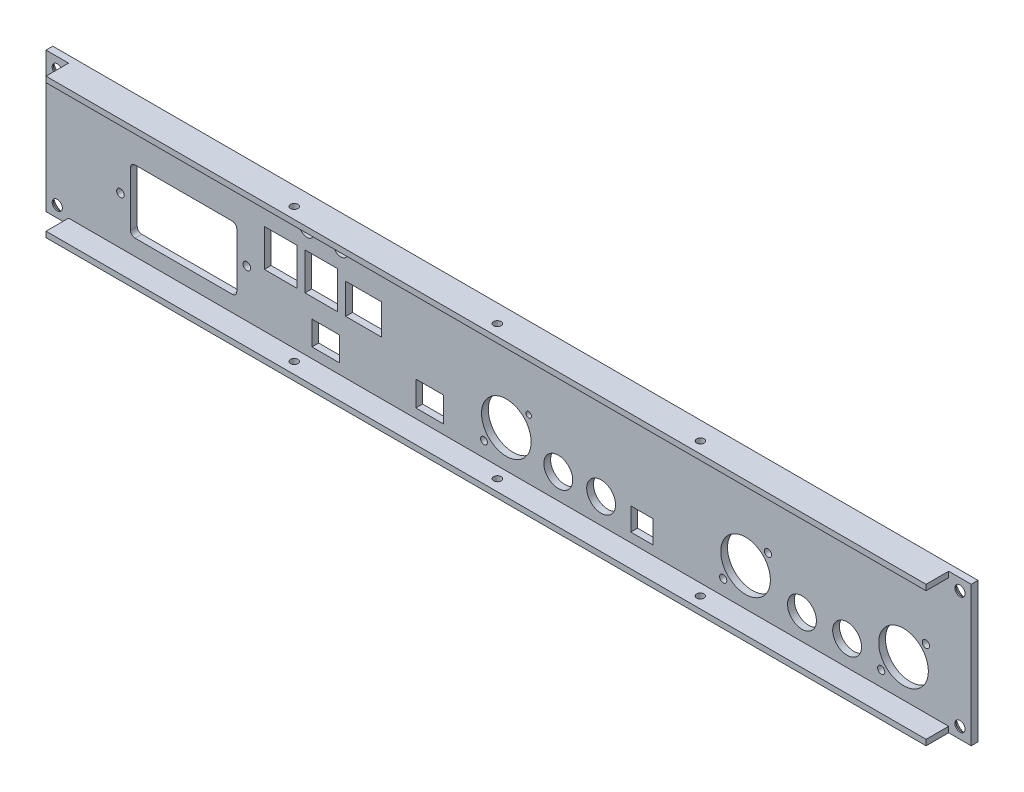
SolidWorks part; units mm, degrees
ref_plane "前基準面" through (0, 0, 0) normal (0, 0, 1) x (1, 0, 0)
ref_plane "上基準面" through (0, 0, 0) normal (0, 1, 0) x (1, 0, 0)
ref_plane "右基準面" through (0, 0, 0) normal (1, 0, 0) x (0, 0, -1)
sketch "草圖1" plane through (0, 0, 0) normal (0, 0, 1) x (1, 0, 0)
  line L1 (-205, -31) -> (205, -31)
  line L2 (-205, -31) -> (-205, 31)
  line L3 (-205, 31) -> (205, 31)
  line L4 (205, -31) -> (205, 31)
  line L5 (-205, -31) -> (205, 31) construction
  line L6 (-205, 31) -> (205, -31) construction
  point P0 (0, 0)
  dimension "D1" = 62
  dimension "D2" = 410
extrude "填料-伸長1" add sketch "草圖1" along normal blind 3
hole_wizard "M4 錐坑平頭螺釘的錐孔1" positions "草圖3" profile "草圖2" countersink size "M4" standard "ISO" end condition through all
sketch "草圖3" plane through (0, 0, 0) normal (0, 0, 1) x (1, 0, 0)
  line L0 (-205, 31) -> (-205, -31) construction
  line L1 (205, -31) -> (205, 31) construction
  line L2 (205, 31) -> (-205, 31) construction
  line L3 (-205, -31) -> (205, -31) construction
  point P0 (-200, 26)
  point P2 (-200, -26)
  point P4 (200, -26)
  point P6 (200, 26)
  dimension "D1" = 5
  dimension "D2" = 5
  dimension "D3" = 5
  dimension "D4" = 5
sketch "草圖2" plane through (-200, 26, 0) normal (1, 0, 0) x (0, 1, 0)
  line L0 (0, 0) -> (0, 3)
  line L1 (0, 3) -> (2.25, 3)
  line L2 (2.25, 3) -> (2.25, 2.45)
  line L3 (2.25, 2.45) -> (4.7, 0)
  line L5 (4.7, 0) -> (0, 0)
  line L6 (-2.25, 2.45) -> (-4.7, 0) construction
  line L11 (0, -6.35) -> (0, 107.95) construction
  dimension "貫穿孔直徑" = 4.5
  dimension "貫穿孔深度" = 3
  dimension "近端錐孔直徑" = 9.4
  dimension "近端錐孔角度" = 90
sketch "草圖5" plane through (0, 0, 3) normal (0, 0, 1) x (1, 0, 0)
  line L0 (205, 31) -> (-205, 31) construction
  line L1 (-195, 31) -> (195, 31)
  line L2 (-195, 31) -> (-195, 28.5)
  line L3 (-195, 28.5) -> (195, 28.5)
  line L4 (195, 31) -> (195, 28.5)
  line L5 (-205, -31) -> (205, -31) construction
  line L6 (-195, -31) -> (195, -31)
  line L7 (-195, -31) -> (-195, -28.5)
  line L8 (-195, -28.5) -> (195, -28.5)
  line L9 (195, -31) -> (195, -28.5)
  line L10 (-205, 31) -> (-205, -31) construction
  line L11 (205, -31) -> (205, 31) construction
  dimension "D1" = 10
  dimension "D2" = 10
  dimension "D3" = 2.5
  dimension "D4" = 2.5
extrude "填料-伸長2" add sketch "草圖5" along normal blind 10
sketch "草圖6" plane through (0, 0, 3) normal (0, 0, 1) x (1, 0, 0)
  line L0 (-195, -31) -> (195, -31) construction
  line L1 (90, -26) -> (-54.018, -26)
  line L2 (90, -26) -> (90, -24.4)
  line L3 (205, -31) -> (205, 31) construction
  line L4 (90, -24.4) -> (-54.018, -24.4)
  line L5 (-54.018, -26) -> (-54.018, -24.4)
  line L6 (54.137, -24.4) -> (63.887, -24.4)
  line L7 (90, -24.4) -> (190, -24.4)
  line L8 (90, -24.4) -> (90, -26)
  line L9 (90, -26) -> (190, -26)
  line L10 (190, -24.4) -> (190, -26)
  line L11 (54.137, -24.4) -> (54.137, -14.35)
  line L12 (54.137, -14.35) -> (63.887, -14.35)
  line L13 (63.887, -24.4) -> (63.887, -14.35)
  line L14 (54.137, -24.4) -> (63.887, -14.35) construction
  line L15 (54.137, -14.35) -> (63.887, -24.4) construction
  line L16 (-205, 31) -> (-205, -31) construction
  line L17 (-41.1434, -24.4) -> (-28.8434, -24.4)
  line L18 (-41.1434, -24.4) -> (-41.1434, -13.3)
  line L19 (-41.1434, -13.3) -> (-28.8434, -13.3)
  line L20 (-28.8434, -24.4) -> (-28.8434, -13.3)
  line L21 (-41.1434, -24.4) -> (-28.8434, -13.3) construction
  line L22 (-41.1434, -13.3) -> (-28.8434, -24.4) construction
  line L23 (-54.018, -24.4) -> (-174.018, -24.4)
  line L24 (-54.018, -24.4) -> (-54.018, -26)
  line L25 (-54.018, -26) -> (-174.018, -26)
  line L26 (-174.018, -24.4) -> (-174.018, -26)
  line L28 (-165.568, -21.45) -> (-122.468, -21.45)
  line L29 (195, -31) -> (205, -31) construction
  line L30 (-167.568, -19.45) -> (-167.568, 4.65)
  line L31 (-165.568, 6.65) -> (-122.468, 6.65)
  line L32 (-120.468, -19.45) -> (-120.468, 4.65)
  line L33 (-167.568, -21.45) -> (-120.468, 6.65) construction
  line L34 (-167.568, 6.65) -> (-120.468, -21.45) construction
  line L35 (-87.168, -24) -> (-74.868, -24)
  line L36 (-87.168, -24) -> (-87.168, -13.3)
  line L37 (-87.168, -13.3) -> (-74.868, -13.3)
  line L38 (-74.868, -24) -> (-74.868, -13.3)
  line L39 (-87.168, -24) -> (-74.868, -13.3) construction
  line L40 (-87.168, -13.3) -> (-74.868, -24) construction
  line L41 (-54.018, -4.8) -> (-110.018, -4.8)
  line L42 (-54.018, -4.8) -> (-54.018, -6.4)
  line L43 (-54.018, -6.4) -> (-110.018, -6.4)
  line L44 (-110.018, -4.8) -> (-110.018, -6.4)
  line L45 (-54.018, -4.8) -> (-110.018, -6.4) construction
  line L46 (-54.018, -6.4) -> (-110.018, -4.8) construction
  line L47 (-56.318, 8.7) -> (-72.218, 8.7)
  line L48 (-56.318, 8.7) -> (-56.318, -4.8)
  line L49 (-56.318, -4.8) -> (-72.218, -4.8)
  line L50 (-72.218, 8.7) -> (-72.218, -4.8)
  line L51 (-56.318, 8.7) -> (-72.218, -4.8) construction
  line L52 (-56.318, -4.8) -> (-72.218, 8.7) construction
  line L53 (-75.768, 11.7) -> (-90.268, 11.7)
  line L54 (-75.768, 11.7) -> (-75.768, -4.8)
  line L55 (-75.768, -4.8) -> (-90.268, -4.8)
  line L56 (-90.268, 11.7) -> (-90.268, -4.8)
  line L57 (-75.768, 11.7) -> (-90.268, -4.8) construction
  line L58 (-75.768, -4.8) -> (-90.268, 11.7) construction
  line L59 (-93.768, 11.7) -> (-108.268, 11.7)
  line L60 (-93.768, 11.7) -> (-93.768, -4.8)
  line L61 (-93.768, -4.8) -> (-108.268, -4.8)
  line L62 (-108.268, 11.7) -> (-108.268, -4.8)
  line L63 (-93.768, 11.7) -> (-108.268, -4.8) construction
  line L64 (-93.768, -4.8) -> (-108.268, 11.7) construction
  circle A0 centre (175, -11.9) radius 11
  circle A1 centre (150, -17.35) radius 6.4
  circle A2 centre (130, -17.35) radius 6.4
  circle A3 centre (105, -11.9) radius 11
  circle A4 centre (114.9, -2) radius 1.6
  circle A5 centre (95.1, -21.8) radius 1.6
  circle A6 centre (184.9, -2) radius 1.6
  circle A7 centre (165.1, -21.8) radius 1.6
  circle A8 centre (41.0034, -17.35) radius 6.4
  circle A9 centre (22.0042, -17.35) radius 6.4
  circle A10 centre (-1.0082, -11.9) radius 11
  circle A11 centre (8.8918, -2) radius 1.2179
  circle A12 centre (-10.9082, -21.8) radius 1.5079
  circle A13 centre (-116.018, -7.4) radius 1.7
  circle A14 centre (-172.018, -7.4) radius 1.7
  arc A15 (-120.468, 4.65) -> (-122.468, 6.65) centre (-122.468, 4.65) ccw
  arc A16 (-122.468, -21.45) -> (-120.468, -19.45) centre (-122.468, -19.45) ccw
  arc A17 (-167.568, -19.45) -> (-165.568, -21.45) centre (-165.568, -19.45) ccw
  arc A18 (-167.568, 4.65) -> (-165.568, 6.65) centre (-165.568, 4.65) cw
  circle A20 centre (-89.3657, 20.2) radius 3.25
  circle A21 centre (-74.3657, 20.2) radius 3.25
  point P24 (59.012, -19.375)
  point P41 (-34.9934, -18.85)
  point P52 (-144.018, -7.4)
  point P73 (-81.018, -18.65)
  point P78 (-82.018, -5.6)
  point P83 (-64.268, 1.95)
  point P88 (-83.018, 3.45)
  point P93 (-101.018, 3.45)
  dimension "D11" = 22
  dimension "D12" = 22
  dimension "D13" = 12.8
  dimension "D14" = 12.8
  dimension "D22" = 3.2
  dimension "D23" = 3.2
  dimension "D24" = 3.2
  dimension "D25" = 3.2
  dimension "D37" = 22
  dimension "D45" = 12.8
  dimension "D46" = 12.8
  dimension "D61" = 2
  dimension "D68" = 3.4
  dimension "D78" = 3.4
  dimension "D79" = 18
  dimension "D82" = 6.5
  dimension "D83" = 6.5
  dimension "D2" = 1.6
  dimension "D3" = 25
  dimension "D4" = 20
  dimension "D5" = 25
  dimension "D6" = 30
  dimension "D7" = 100
  dimension "D8" = 15
  dimension "D9" = 19.8
  dimension "D10" = 19.8
  dimension "D15" = 15
  dimension "D16" = 9.9
  dimension "D17" = 19.8
  dimension "D18" = 19.8
  dimension "D19" = 9.9
  dimension "D20" = 9.9
  dimension "D21" = 9.9
  dimension "D26" = 1.6
  dimension "D27" = 30.988
  dimension "D28" = 9.75
  dimension "D29" = 10.05
  dimension "D30" = 5
  dimension "D31" = 12.5
  dimension "D32" = 12.5
  dimension "D33" = 7.05
  dimension "D34" = 7.05
  dimension "D35" = 48.9966
  dimension "D36" = 67.9958
  dimension "D38" = 19.8
  dimension "D39" = 12.5
  dimension "D40" = 9.9
  dimension "D41" = 19.8
  dimension "D42" = 9.9
  dimension "D43" = 7.05
  dimension "D44" = 7.05
  dimension "D47" = 144.018
  dimension "D48" = 124.9934
  dimension "D49" = 91.0082
  dimension "D50" = 12.3
  dimension "D51" = 11.1
  dimension "D52" = 120
  dimension "D53" = 1.6
  dimension "D54" = 30.982
  dimension "D55" = 90
  dimension "D56" = 47.1
  dimension "D57" = 28.1
  dimension "D58" = 17
  dimension "D59" = 28
  dimension "D60" = 56
  dimension "D62" = 27
  dimension "D63" = 11.1
  dimension "D64" = 10.7
  dimension "D65" = 12.3
  dimension "D66" = 1.6
  dimension "D67" = 56
  dimension "D69" = 10.25
  dimension "D70" = 29
  dimension "D71" = 47
  dimension "D72" = 14.5
  dimension "D73" = 14.5
  dimension "D74" = 15.9
  dimension "D75" = 13.5
  dimension "D76" = 16.5
  dimension "D77" = 16.5
  dimension "D81" = 15
  dimension "D84" = 25
extrude "除料-伸長1" cut sketch "草圖6" against normal blind 10 contours A18 L30 A17 L28 A16 L32 A15 L31 | A14 | A13 | L47 L50 L41 L48 | L53 L56 L41 L54 | L59 L62 L41 L60 | L35 L38 L37 L36 | L4 L20 L19 L18 | A10 | A11 | A9 | A12 | L4 L13 L12 L11 | A8 | A3 | A2 | A1 | A0 | A6 | A7 | A4 | A5 | A21 | A20
sketch "草圖12" plane through (0, 31, 0) normal (0, 1, 0) x (1, 0, 0)
  line L0 (-195, -13) -> (0, -13)
  line L1 (195, -13) -> (-195, -13) construction
  line L2 (0, -13) -> (195, -13)
hole_wizard "M4 螺紋孔1" positions "草圖13" profile "草圖14" tap size "M4" standard "ISO" end condition through all
sketch "草圖13" plane through (0, 31, 0) normal (0, 1, 0) x (1, 0, 0)
  line L7 (-195, -13) -> (-195, -3) construction
  point P0 (0, -8)
  point P2 (-90, -8)
  point P4 (90, -8)
  dimension "D1" = 5
  dimension "D2" = 90
  dimension "D3" = 90
  dimension "D4" = 195
sketch "草圖14" plane through (0, 31, 8) normal (1, 0, 0) x (0, 0, 1)
  line L0 (0, 0) -> (0, 62)
  line L1 (0, 62) -> (1.65, 62)
  line L2 (1.65, 62) -> (1.65, 0)
  line L5 (1.65, 0) -> (0, 0)
  line L11 (0, -6.35) -> (0, 107.95) construction
  dimension "貫穿螺孔鑽直徑" = 3.3
  dimension "貫穿螺孔鑽深度" = 62
cosmetic thread "鑽孔螺紋1" parameters "D2"=4
cosmetic thread "鑽孔螺紋2" parameters "D2"=4
cosmetic thread "鑽孔螺紋3" parameters "D2"=4
